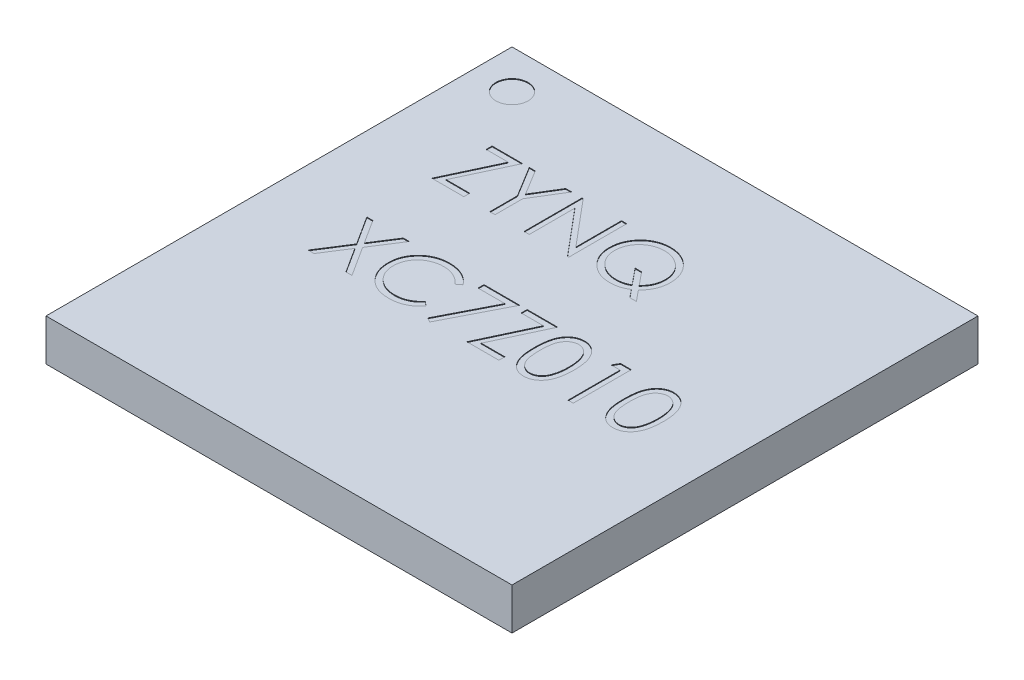
SolidWorks part; units mm, degrees
ref_plane "Front Plane" through (0, 0, 0) normal (0, 0, 1) x (1, 0, 0)
ref_plane "Top Plane" through (0, 0, 0) normal (0, 1, 0) x (1, 0, 0)
ref_plane "Right Plane" through (0, 0, 0) normal (1, 0, 0) x (0, 0, -1)
sketch "Sketch1" plane through (0, 0, 0) normal (0, 1, 0) x (1, 0, 0)
  line L1 (0, 0) -> (17.0002, 0)
  line L2 (0, 0) -> (0, 17.0002)
  line L3 (0, 17.0002) -> (17.0002, 17.0002)
  line L4 (17.0002, 0) -> (17.0002, 17.0002)
  dimension "D1" = 17.0002
extrude "Boss-Extrude1" add sketch "Sketch1" along normal blind 1.52
sketch "Sketch2" plane through (0, 1.52, 0) normal (0, 1, 0) x (1, 0, 0)
  line L0 (1.4134, 17.0002) -> (1.4134, 15.5868) construction
  line L1 (17.0002, 17.0002) -> (0, 17.0002) construction
  line L2 (1.4134, 15.5868) -> (0, 15.5868) construction
  line L3 (0, 17.0002) -> (0, 0) construction
  circle A0 centre (1.4134, 15.5868) radius 0.5851
  text T0 "ZYNQ\r\nXC7Z010" font "Century Gothic" height in points 8
extrude "Cut-Extrude1" cut sketch "Sketch2" against normal blind 0.0254
